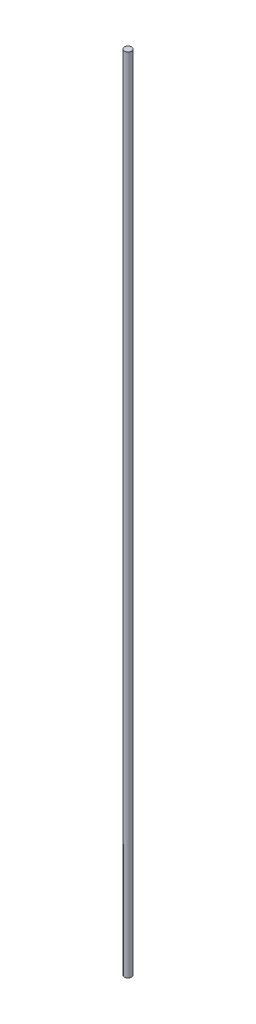
SolidWorks part; units mm, degrees
ref_plane "Front Plane" through (0, 0, 0) normal (0, 0, 1) x (1, 0, 0)
ref_plane "Top Plane" through (0, 0, 0) normal (0, 1, 0) x (1, 0, 0)
ref_plane "Right Plane" through (0, 0, 0) normal (1, 0, 0) x (0, 0, -1)
sketch "Sketch1" plane through (0, 0, 0) normal (0, 1, 0) x (1, 0, 0)
  circle A0 centre (0, 0) radius 1
  dimension "D1" = 2
extrude "Boss-Extrude1" add sketch "Sketch1" along normal blind 220
